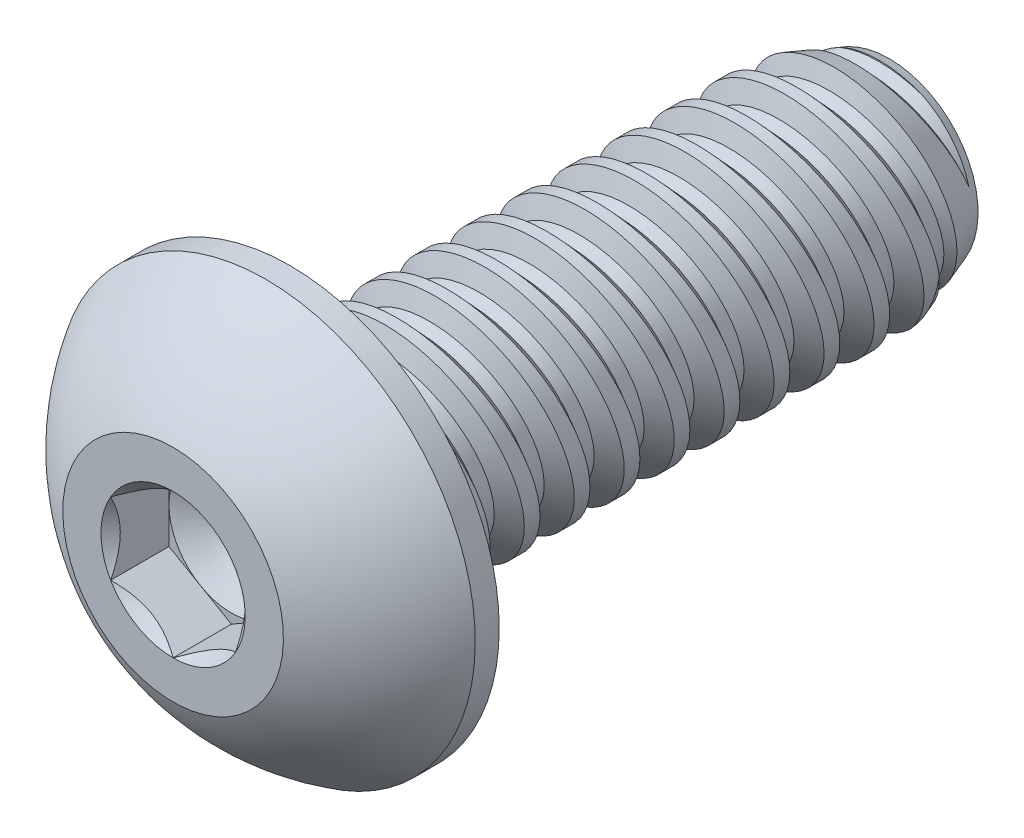
SolidWorks part; units mm, degrees
ref_plane "Front" through (0, 0, 0) normal (0, 0, 1) x (1, 0, 0)
ref_plane "Top" through (0, 0, 0) normal (0, 1, 0) x (1, 0, 0)
ref_plane "Right" through (0, 0, 0) normal (1, 0, 0) x (0, 0, -1)
sketch "Sketch1" plane through (0, 0, 0) normal (1, 0, 0) x (0, 0, -1)
  line L0 (0, 0) -> (-1.8542, 0) construction
  line L1 (0, 0) -> (9.525, 0)
  line L2 (0, 0) -> (0, 1.7526)
  line L3 (0, 1.7526) -> (9.525, 1.7526)
  line L4 (9.525, 0) -> (9.525, 1.7526)
  line L5 (0, -1.7526) -> (9.525, -1.7526) construction
  dimension "D1" = 9.525
  dimension "Thread Dia" = 3.5052
  dimension "Length" = 9.525
  dimension "Head Height" = 1.8542
revolve "Revolve1" add sketch "Sketch1" angle 360 about L0
ref_plane "Plane1" through (0, 0, 1.8542) normal (0, 0, 1) x (1, 0, 0)
sketch "Sketch2" plane through (0, 0, 0) normal (1, 0, 0) x (0, 0, -1)
  line L0 (0, 1.7526) -> (0, -1.7526) construction
  line L1 (0, -1.7526) -> (0.7938, -1.7526) construction
  line L2 (0.7938, -1.7526) -> (0, 1.7526) construction
  line L3 (0, 1.7526) -> (0.0968, 1.7745) construction
  line L4 (0.0968, 1.7745) -> (0.7741, 1.9279)
  line L5 (0.7741, 1.9279) -> (0.6271, 1.4541)
  line L6 (0.6271, 1.4541) -> (0.4336, 1.4103)
  line L7 (0.4336, 1.4103) -> (0.0968, 1.7745)
  line L8 (0.5303, 1.4322) -> (0.4355, 1.8512) construction
  line L9 (0, -1.7526) -> (9.525, -1.7526) construction
  line L10 (0, 1.7526) -> (9.525, 1.7526) construction
  line L12 (0.4578, 1.7526) -> (1.2515, -1.7526) construction
  line L13 (0, -0.1935) -> (1.7093, 0.1935) construction
  line L15 (0, 0) -> (0, 1.7526) construction
  point P19 (0.8547, 0)
  dimension "D1" = 60
  dimension "Thread Pitch" = 0.7937
  dimension "D2" = 0.0992
  dimension "D3" = 0.1984
  dimension "D4" = 0.7937
revolve "Cut-Revolve1" cut sketch "Sketch2" angle 360 about L13
sketch "Sketch3" plane through (0, 0, 0) normal (1, 0, 0) x (0, 0, -1)
  line L0 (9.525, 1.4103) -> (8.5845, 1.7526)
  line L1 (8.5845, 1.7526) -> (9.525, 1.7526)
  line L2 (9.525, 1.7526) -> (9.525, 1.4103)
  line L3 (0, 1.7526) -> (9.525, 1.7526) construction
  line L4 (9.525, 0) -> (9.525, 1.7526) construction
  line L5 (8.5845, 0) -> (0, 0) construction
  line L6 (8.5845, 1.7526) -> (8.5845, -1.7526) construction
  line L7 (0, -1.7526) -> (9.525, -1.7526) construction
  dimension "D1" = 20
  dimension "D2" = 3.5052
revolve "Cut-Revolve2" cut sketch "Sketch3" angle 360 about L5
pattern_linear "LPattern1" count 12 spacing 0.7937 along (0, 0, 1)
pattern_linear "LPattern2" count 2 spacing 0.7937 along (0, 0, 1)
sketch "Sketch4" plane through (0, 0, 0) normal (0, 0, 1) x (1, 0, 0)
  circle A0 centre (0, 0) radius 3.3274
  dimension "Head Dia" = 6.6548
extrude "Extrude1" add sketch "Sketch4" along normal up to surface (1.8542 mm away)
sketch "Sketch9" plane through (0, 0, 0) normal (1, 0, 0) x (0, 0, -1)
  line L0 (0, 3.3274) -> (-0.381, 3.3274)
  line L1 (0, 3.3274) -> (0, 3.7084)
  line L2 (0, 3.7084) -> (-2.2352, 3.7084)
  line L3 (0, 0) -> (-1.8542, 0) construction
  line L4 (-2.2352, 3.7084) -> (-2.2352, 1.7526)
  line L5 (-2.2352, 1.7526) -> (-1.8542, 1.7526)
  line L6 (0, 0) -> (0, 1.7526) construction
  line L10 (0, 3.3274) -> (-1.8542, 3.3274) construction
  line L11 (0, 1.7526) -> (9.525, 1.7526) construction
  line L12 (-1.8542, 3.3274) -> (-1.8542, -3.3274) construction
  arc A0 (-1.8542, 1.7526) -> (-0.381, 3.3274) centre (1.5976, 0) cw
  dimension "Side Head Height" = 0.381
revolve "Cut-Revolve3" cut sketch "Sketch9" angle 360 about L3
sketch "Sketch6" plane through (0, 0, 1.8542) normal (0, 0, 1) x (1, 0, 0)
  line L1 (0, -1.1457) -> (0.9922, -0.5728)
  line L2 (0.9922, -0.5728) -> (0.9922, 0.5728)
  line L3 (0.9922, 0.5728) -> (0, 1.1457)
  line L4 (0, 1.1457) -> (-0.9922, 0.5728)
  line L5 (-0.9922, 0.5728) -> (-0.9922, -0.5728)
  line L6 (-0.9922, -0.5728) -> (0, -1.1457)
  circle A0 centre (0, 0) radius 0.9922 construction
  dimension "Hex" = 1.9844
extrude "Cut-Extrude1" cut sketch "Sketch6" against normal blind 0.9271
sketch "Sketch7" plane through (0, 0, 1.8542) normal (0, 0, 1) x (1, 0, 0)
  circle A0 centre (0, 0) radius 1.1457
extrude "Cut-Extrude4" cut sketch "Sketch7" against normal blind 0.9271 draft 45
sketch "Sketch8" plane through (0, 0, 0.9271) normal (0, 0, 1) x (1, 0, 0)
  circle A0 centre (0, 0) radius 0.9922 construction
  circle A1 centre (0, 0) radius 0.9922
extrude "Cut-Extrude5" cut sketch "Sketch8" against normal blind 0.309 draft 60
equation "\"D2@Sketch2\"=\"Thread Pitch@Sketch2\"/8"
equation "\"D3@Sketch2\"=\"Thread Pitch@Sketch2\"/4"
equation "\"D4@Sketch2\"=\"Thread Pitch@Sketch2\""
equation "\"D3@LPattern1\"=\"Thread Pitch@Sketch2\""
equation "\"D1@Cut-Extrude1\"=\"Head Height@Sketch1\"/2"
equation "\"D1@Cut-Extrude4\"=\"D1@Cut-Extrude1\""
equation "\"D1@Cut-Extrude5\"=\"D1@Cut-Extrude1\"/3"
equation "\"D1@LPattern1\"=\"D1@Sketch1\"/\"Thread Pitch@Sketch2\""
equation "\"D3@LPattern2\"=\"Thread Pitch@Sketch2\""
